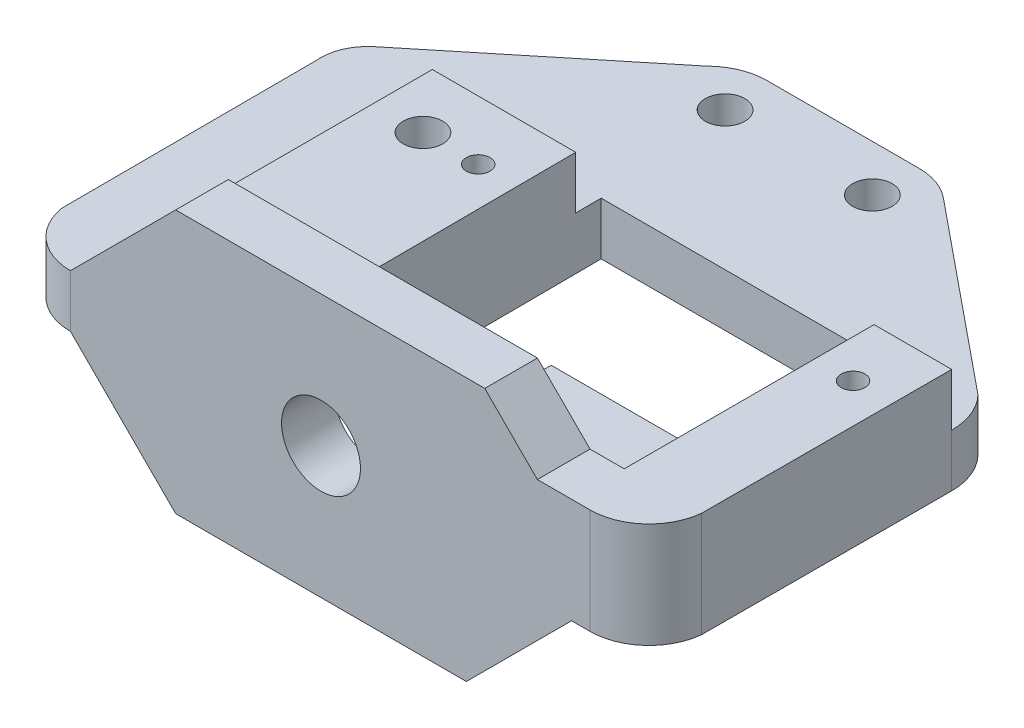
SolidWorks part; units mm, degrees
ref_plane "Alzado" through (0, 0, 0) normal (0, 0, 1) x (1, 0, 0)
ref_plane "Planta" through (0, 0, 0) normal (0, 1, 0) x (1, 0, 0)
ref_plane "Vista lateral" through (0, 0, 0) normal (1, 0, 0) x (0, 0, -1)
sketch "Croquis1" plane through (0, 0, 0) normal (0, 1, 0) x (1, 0, 0)
  line L0 (-19.2453, -19.1284) -> (20.2547, -19.1284)
  line L1 (24.7153, -15.1294) -> (24.7547, 3.8716)
  line L2 (23.4367, 7.1896) -> (9.1326, 18.8585)
  line L3 (6.2881, 19.8716) -> (-5.2786, 19.8716)
  line L4 (-8.5453, 18.5142) -> (-22.4272, 7.1896)
  line L5 (-23.6899, -15.3324) -> (-23.7453, 4.0076)
  line L6 (-3.8453, 5.8216) -> (-3.7453, -15.1244)
  line L7 (-3.8453, 5.8216) -> (18.8547, 5.8216)
  line L8 (5.2547, -7.0784) -> (18.8547, -7.0784)
  line L9 (18.8547, 5.8216) -> (18.8547, -7.0784)
  line L10 (5.2547, -7.0784) -> (5.2547, -15.1244)
  line L11 (5.2547, -15.1244) -> (-3.7453, -15.1244)
  arc A0 (20.2547, -19.1284) -> (24.7153, -15.1294) centre (20.2547, -14.6412) ccw
  arc A1 (24.7547, 3.8716) -> (23.4367, 7.1896) centre (19.9444, 3.8816) ccw
  arc A2 (9.1326, 18.8585) -> (6.2881, 19.8716) centre (6.2881, 15.3716) ccw
  arc A3 (-5.2786, 19.8716) -> (-8.5453, 18.5142) centre (-5.2786, 15.2623) ccw
  arc A4 (-22.4272, 7.1896) -> (-23.7453, 4.0076) centre (-20.1306, 4.3744) ccw
  arc A5 (-19.2453, -19.1284) -> (-23.6899, -15.3324) centre (-19.2453, -14.6284) cw
  circle A6 centre (-10.9453, -0.6284) radius 1.5
  circle A7 centre (-6.7453, -0.6284) radius 0.9
  circle A8 centre (21.7547, -0.6284) radius 0.9
  circle A9 centre (6.2547, 16.3416) radius 1.5
  circle A10 centre (-4.9453, 16.3416) radius 1.5
extrude "Saliente-Extruir1" add sketch "Croquis1" along normal blind 4
sketch "Croquis2" plane through (0, 4, 0) normal (0, 1, 0) x (1, 0, 0)
  line L0 (-3.8453, 5.8216) -> (-3.7453, -15.1244) construction
  line L1 (-3.836, 3.8756) -> (-14.736, 3.8756)
  line L4 (-14.736, 3.8756) -> (-14.736, -15.1244)
  line L6 (-3.836, 3.8756) -> (-3.7453, -15.1244)
  line L7 (24.7547, 3.8716) -> (18.8547, 3.8716)
  line L11 (-19.2453, -19.1284) -> (-19.2453, -15.1244)
  line L12 (-19.2453, -15.1244) -> (-14.736, -15.1244)
  line L13 (-19.2453, -19.1284) -> (20.2547, -19.1284)
  line L14 (-3.7453, -15.1244) -> (18.8547, -15.1244)
  line L15 (18.8547, -15.1244) -> (18.8547, 3.8716)
  line L16 (18.8547, -7.0784) -> (18.8547, 5.8216) construction
  line L17 (-3.7453, -15.1244) -> (5.2547, -15.1244) construction
  arc A0 (20.2547, -19.1284) -> (24.7153, -15.1294) centre (20.2547, -14.6412) ccw construction
  arc A1 (20.2547, -19.1284) -> (24.7153, -15.1294) centre (20.2547, -14.6412) ccw
  circle A2 centre (21.7547, -0.6284) radius 0.9 construction
  circle A3 centre (-6.7453, -0.6284) radius 0.9 construction
  circle A4 centre (-10.9453, -0.6284) radius 1.5 construction
  circle A5 centre (21.7547, -0.6284) radius 0.9
  circle A6 centre (-6.7453, -0.6284) radius 0.9
  circle A7 centre (-10.9453, -0.6284) radius 1.5
  line M11 (-19.2453, -19.1284) -> (20.2547, -19.1284)
  arc M12 (20.2547, -19.1284) -> (24.7153, -15.1294) centre (20.2547, -14.6412) ccw
  line M13 (24.7153, -15.1294) -> (24.7547, 3.8716)
  line M23 (18.8547, 5.8216) -> (18.8547, -7.0784)
  line M26 (5.2547, -15.1244) -> (-3.7453, -15.1244)
  circle M28 centre (-10.9453, -0.6284) radius 1.5
  circle M29 centre (-6.7453, -0.6284) radius 0.9
  circle M30 centre (21.7547, -0.6284) radius 0.9
  dimension "D1" = 10.9
  dimension "D2" = 19
extrude "Saliente-Extruir2" add sketch "Croquis2" along normal blind 4 contours L15 L14 L6 L1 L4 L12 L11 L7 M26 M11 M12 M13 M23 M28 M30 M29
sketch "Croquis3" plane through (0, 8, 0) normal (0, 1, 0) x (1, 0, 0)
  line L0 (-19.2453, -19.1284) -> (20.2547, -19.1284) construction
  line L1 (-19.2453, -15.1244) -> (16.2547, -15.1244)
  line L2 (-19.2453, -15.1244) -> (-19.2453, -19.1284)
  line L3 (-19.2453, -19.1284) -> (16.2547, -19.1284)
  line L4 (16.2547, -15.1244) -> (16.2547, -19.1284)
  line L5 (18.8547, -15.1244) -> (18.8547, 3.8716) construction
  dimension "D1" = 2.6
extrude "Saliente-Extruir3" add sketch "Croquis3" along normal blind 4
sketch "Croquis4" plane through (0, 0, 0) normal (0, -1, 0) x (1, 0, 0)
  line L0 (-19.2453, 19.1284) -> (20.2547, 19.1284) construction
  line L1 (18.8547, 19.1284) -> (-19.2453, 19.1284)
  line L2 (18.8547, 19.1284) -> (18.8547, 15.1244)
  line L3 (18.8547, 15.1244) -> (-19.2453, 15.1244)
  line L4 (-19.2453, 19.1284) -> (-19.2453, 15.1244)
  line L5 (18.8547, 7.0784) -> (18.8547, -5.8216) construction
  line L6 (-3.7453, 15.1244) -> (5.2547, 15.1244) construction
extrude "Saliente-Extruir4" add sketch "Croquis4" along normal blind 8
sketch "Croquis5" plane through (0, 0, 19.1284) normal (0, 0, 1) x (1, 0, 0)
  line L0 (16.2547, 8) -> (12.2547, 12)
  line L1 (-19.2453, 12) -> (16.2547, 12) construction
  line L2 (12.2547, 12) -> (16.2547, 12)
  line L3 (16.2547, 12) -> (16.2547, 8)
  line L4 (-19.2453, 4) -> (-11.2453, 12)
  line L5 (-11.2453, 12) -> (-19.2453, 12)
  line L6 (-19.2453, 12) -> (-19.2453, 4)
  line L7 (-19.2453, 0) -> (-11.2453, -8)
  line L8 (18.8547, -8) -> (-19.2453, -8) construction
  line L9 (-11.2453, -8) -> (-19.2453, -8)
  line L10 (-19.2453, -8) -> (-19.2453, 0)
  line L11 (18.8547, -8) -> (10.8547, -8)
  line L12 (10.8547, -8) -> (18.8547, 0)
  line L13 (18.8547, -8) -> (18.8547, 0) construction
  line L14 (18.8547, 0) -> (18.8547, -8)
  line L15 (-19.2453, 4) -> (-19.2453, 0) construction
  circle A0 centre (-0.1953, 2) radius 3
  point P29 (-19.2453, 2)
  dimension "D4" = 6
  dimension "D1" = 4
  dimension "D2" = 8
  dimension "D3" = 8
  dimension "D5" = 19.05
extrude "Cortar-Extruir1" cut sketch "Croquis5" against normal blind 8
